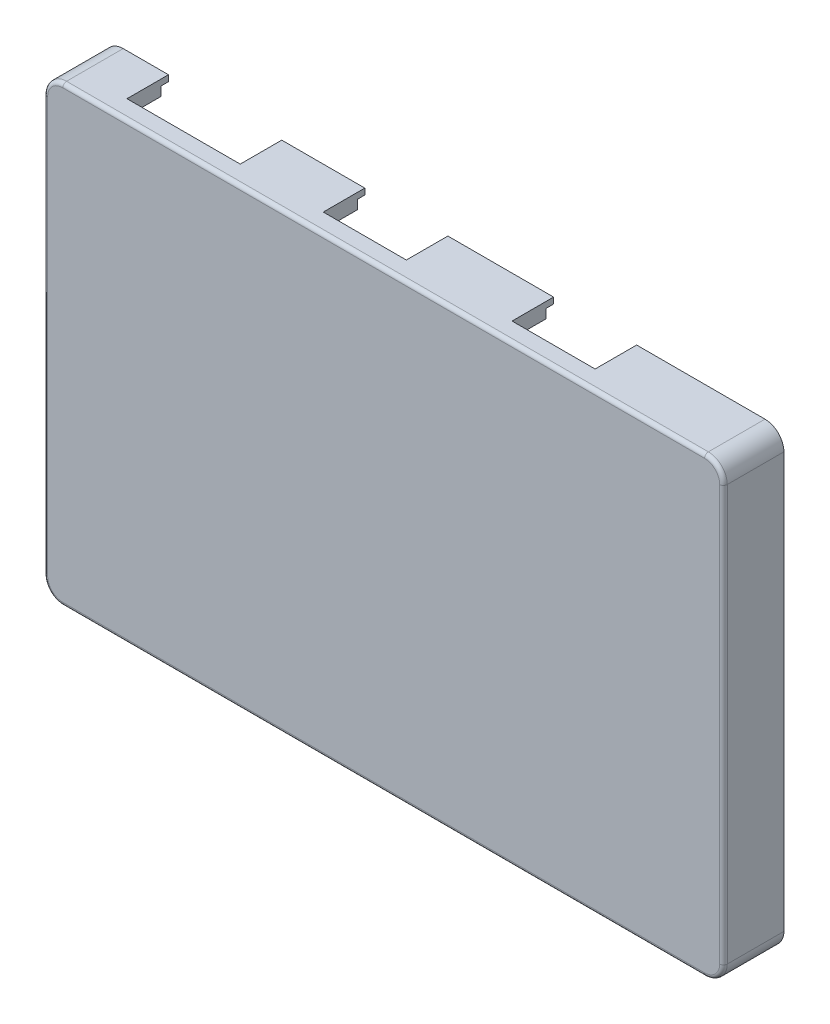
SolidWorks part; units mm, degrees
ref_plane "Спереди" through (0, 0, 0) normal (0, 0, 1) x (1, 0, 0)
ref_plane "Сверху" through (0, 0, 0) normal (0, 1, 0) x (1, 0, 0)
ref_plane "Справа" through (0, 0, 0) normal (1, 0, 0) x (0, 0, -1)
sketch "Эскиз1" plane through (0, 0, 0) normal (0, 0, 1) x (1, 0, 0)
  line L1 (-33.6522, 21.2609) -> (56.3478, 21.2609)
  line L2 (-33.6522, 21.2609) -> (-33.6522, -38.7391)
  line L3 (-33.6522, -38.7391) -> (56.3478, -38.7391)
  line L4 (56.3478, 21.2609) -> (56.3478, -38.7391)
  dimension "D1" = 90
  dimension "D2" = 60
extrude "Бобышка-Вытянуть1" add sketch "Эскиз1" along normal blind 2
sketch "Эскиз2" plane through (0, 0, 0) normal (0, 0, -1) x (-1, 0, 0)
  line L0 (-56.3478, 21.2609) -> (33.6522, 21.2609) construction
  line L1 (28.6522, -16.7391) -> (-21.3478, -16.7391)
  line L2 (28.6522, -16.7391) -> (28.6522, 18.2609)
  line L3 (28.6522, 18.2609) -> (-21.3478, 18.2609)
  line L4 (-21.3478, -16.7391) -> (-21.3478, 18.2609)
  line L5 (33.6522, 21.2609) -> (33.6522, -38.7391) construction
  dimension "D1" = 35
  dimension "D2" = 50
  dimension "D3" = 3
  dimension "D4" = 5
extrude "Бобышка-Вытянуть2" add sketch "Эскиз2" along normal blind 1
sketch "Эскиз3" plane through (0, 0, -1) normal (0, 0, -1) x (-1, 0, 0)
  line L0 (28.6522, -16.7391) -> (28.6522, 18.2609) construction
  line L1 (24.6522, -0.7391) -> (10.6522, -0.7391)
  line L2 (24.6522, -0.7391) -> (24.6522, 12.2609)
  line L3 (24.6522, 12.2609) -> (10.6522, 12.2609)
  line L4 (10.6522, -0.7391) -> (10.6522, 12.2609)
  line L5 (28.6522, 18.2609) -> (-21.3478, 18.2609) construction
  dimension "D1" = 14
  dimension "D2" = 13
  dimension "D3" = 4
  dimension "D4" = 6
extrude "Бобышка-Вытянуть3" add sketch "Эскиз3" along normal blind 10
sketch "Эскиз4" plane through (0, 0, -1) normal (0, 0, -1) x (-1, 0, 0)
  line L0 (28.6522, 18.2609) -> (-21.3478, 18.2609) construction
  line L1 (-1.3478, 9.2609) -> (-11.3478, 9.2609)
  line L2 (-1.3478, 9.2609) -> (-1.3478, 21.2609)
  line L3 (-1.3478, 21.2609) -> (-11.3478, 21.2609)
  line L4 (-11.3478, 9.2609) -> (-11.3478, 21.2609)
  line L5 (28.6522, -16.7391) -> (28.6522, 18.2609) construction
  dimension "D1" = 10
  dimension "D2" = 12
  dimension "D3" = 3
  dimension "D4" = 30
extrude "Бобышка-Вытянуть4" add sketch "Эскиз4" along normal blind 5
sketch "Эскиз5" plane through (0, 0, 0) normal (0, 0, -1) x (-1, 0, 0)
  line L0 (-56.3478, -38.7391) -> (-56.3478, 21.2609) construction
  line L1 (-25.3478, -7.7391) -> (-51.3478, -7.7391)
  line L2 (-25.3478, -7.7391) -> (-25.3478, 18.2609)
  line L3 (-25.3478, 18.2609) -> (-51.3478, 18.2609)
  line L4 (-51.3478, -7.7391) -> (-51.3478, 18.2609)
  line L5 (-56.3478, 21.2609) -> (33.6522, 21.2609) construction
  dimension "D1" = 26
  dimension "D2" = 26
  dimension "D3" = 5
  dimension "D4" = 3
extrude "Бобышка-Вытянуть5" add sketch "Эскиз5" along normal blind 1
sketch "Эскиз6" plane through (0, 0, -1) normal (0, 0, -1) x (-1, 0, 0)
  line L0 (-25.3478, -7.7391) -> (-25.3478, 18.2609) construction
  line L1 (-26.3478, 9.2609) -> (-36.3478, 9.2609)
  line L2 (-26.3478, 9.2609) -> (-26.3478, 19.2609)
  line L3 (-26.3478, 19.2609) -> (-36.3478, 19.2609)
  line L4 (-36.3478, 9.2609) -> (-36.3478, 19.2609)
  line L5 (-25.3478, 18.2609) -> (-51.3478, 18.2609) construction
  dimension "D1" = 10
  dimension "D2" = 10
  dimension "D3" = 1
  dimension "D4" = 1
extrude "Бобышка-Вытянуть6" add sketch "Эскиз6" along normal blind 7
sketch "Эскиз7" plane through (0, 0, 0) normal (0, 0, -1) x (-1, 0, 0)
  line L0 (-21.3478, -16.7391) -> (28.6522, -16.7391) construction
  line L1 (6.8938, -35.7391) -> (-36.1062, -35.7391)
  line L2 (6.8938, -35.7391) -> (6.8938, -17.7391)
  line L3 (6.8938, -17.7391) -> (-36.1062, -17.7391)
  line L4 (-36.1062, -35.7391) -> (-36.1062, -17.7391)
  dimension "D1" = 18
  dimension "D2" = 43
  dimension "D3" = 1
extrude "Бобышка-Вытянуть7" add sketch "Эскиз7" along normal blind 1
sketch "Эскиз8" plane through (0, 0, 0) normal (0, 0, -1) x (-1, 0, 0)
  line L0 (33.6522, -38.7391) -> (-56.3478, -38.7391) construction
  line L1 (-56.3478, -38.7391) -> (-54.3478, -38.7391)
  line L2 (-56.3478, -38.7391) -> (-56.3478, 21.2609)
  line L3 (-56.3478, 21.2609) -> (-54.3478, 21.2609)
  line L4 (-54.3478, -38.7391) -> (-54.3478, 21.2609)
  line L5 (-56.3478, 21.2609) -> (33.6522, 21.2609) construction
  line L6 (-56.3478, -38.7391) -> (-56.3478, 21.2609) construction
  point P10 (0, 0)
  dimension "D1" = 2
  dimension "D2" = 0
  dimension "D3" = 0
  dimension "D4" = 0
extrude "Бобышка-Вытянуть8" add sketch "Эскиз8" along normal blind 5
sketch "Эскиз9" plane through (0, 0, 0) normal (0, 0, -1) x (-1, 0, 0)
  line L0 (-54.3478, -38.7391) -> (-54.3478, 21.2609) construction
  line L1 (-54.3478, -38.7391) -> (33.6522, -38.7391)
  line L2 (-54.3478, -38.7391) -> (-54.3478, -36.7391)
  line L3 (-54.3478, -36.7391) -> (33.6522, -36.7391)
  line L4 (33.6522, -38.7391) -> (33.6522, -36.7391)
  line L5 (33.6522, -38.7391) -> (-54.3478, -38.7391) construction
  line L6 (33.6522, 21.2609) -> (33.6522, -38.7391) construction
  dimension "D1" = 2
  dimension "D2" = 0
  dimension "D3" = 0
  dimension "D4" = 0
extrude "Бобышка-Вытянуть9" add sketch "Эскиз9" along normal blind 5
sketch "Эскиз10" plane through (0, 0, 0) normal (0, 0, -1) x (-1, 0, 0)
  line L0 (33.6522, -36.7391) -> (-54.3478, -36.7391) construction
  line L1 (31.6522, -36.7391) -> (33.6522, -36.7391)
  line L2 (31.6522, -36.7391) -> (31.6522, 21.2609)
  line L3 (31.6522, 21.2609) -> (33.6522, 21.2609)
  line L4 (33.6522, -36.7391) -> (33.6522, 21.2609)
  line L5 (33.6522, 21.2609) -> (33.6522, -36.7391) construction
  line L6 (-54.3478, 21.2609) -> (33.6522, 21.2609) construction
  dimension "D1" = 2
  dimension "D2" = 0
  dimension "D3" = 0
  dimension "D4" = 0
extrude "Бобышка-Вытянуть10" add sketch "Эскиз10" along normal blind 5
sketch "Эскиз11" plane through (0, 0, 0) normal (0, 0, -1) x (-1, 0, 0)
  line L0 (-54.3478, -36.7391) -> (-54.3478, 21.2609) construction
  line L1 (-54.3478, 19.2609) -> (31.6522, 19.2609)
  line L2 (-54.3478, 19.2609) -> (-54.3478, 21.2609)
  line L3 (-54.3478, 21.2609) -> (31.6522, 21.2609)
  line L4 (31.6522, 19.2609) -> (31.6522, 21.2609)
  line L5 (-54.3478, 21.2609) -> (31.6522, 21.2609) construction
  line L6 (31.6522, 21.2609) -> (31.6522, -36.7391) construction
  dimension "D1" = 2
  dimension "D2" = 0
  dimension "D3" = 0
  dimension "D4" = 0
extrude "Бобышка-Вытянуть11" add sketch "Эскиз11" along normal blind 5
sketch "Эскиз12" plane through (0, 0, -5) normal (0, 0, -1) x (-1, 0, 0)
  line L0 (-56.3478, -38.7391) -> (33.6522, -38.7391) construction
  line L1 (-56.3478, -38.7391) -> (-55.5478, -38.7391)
  line L2 (-56.3478, -38.7391) -> (-56.3478, 21.2609)
  line L3 (-56.3478, 21.2609) -> (-55.5478, 21.2609)
  line L4 (-55.5478, -38.7391) -> (-55.5478, 21.2609)
  line L5 (-56.3478, 21.2609) -> (-56.3478, -38.7391) construction
  line L6 (-56.3478, 21.2609) -> (33.6522, 21.2609) construction
  dimension "D1" = 0.8
  dimension "D2" = 0
  dimension "D3" = 0
  dimension "D4" = 0
extrude "Бобышка-Вытянуть12" add sketch "Эскиз12" along normal blind 1
sketch "Эскиз13" plane through (0, 0, -5) normal (0, 0, -1) x (-1, 0, 0)
  line L0 (-55.5478, -38.7391) -> (33.6522, -38.7391) construction
  line L1 (-55.5478, -38.7391) -> (33.6522, -38.7391)
  line L2 (-55.5478, -38.7391) -> (-55.5478, -37.9391)
  line L3 (-55.5478, -37.9391) -> (33.6522, -37.9391)
  line L4 (33.6522, -38.7391) -> (33.6522, -37.9391)
  line L5 (-55.5478, -38.7391) -> (-55.5478, 21.2609) construction
  line L6 (33.6522, -38.7391) -> (33.6522, 21.2609) construction
  dimension "D1" = 0.8
  dimension "D2" = 0
  dimension "D3" = 0
  dimension "D4" = 0
extrude "Бобышка-Вытянуть13" add sketch "Эскиз13" along normal blind 1
sketch "Эскиз14" plane through (0, 0, -5) normal (0, 0, -1) x (-1, 0, 0)
  line L0 (33.6522, -37.9391) -> (-55.5478, -37.9391) construction
  line L1 (32.8522, -37.9391) -> (33.6522, -37.9391)
  line L2 (32.8522, -37.9391) -> (32.8522, 21.2609)
  line L3 (32.8522, 21.2609) -> (33.6522, 21.2609)
  line L4 (33.6522, -37.9391) -> (33.6522, 21.2609)
  line L5 (33.6522, -37.9391) -> (33.6522, 21.2609) construction
  line L6 (33.6522, 21.2609) -> (-1.3478, 21.2609) construction
  dimension "D1" = 0.8
  dimension "D2" = 0
  dimension "D3" = 0
  dimension "D4" = 0
extrude "Бобышка-Вытянуть14" add sketch "Эскиз14" along normal blind 1
sketch "Эскиз15" plane through (0, 0, -5) normal (0, 0, -1) x (-1, 0, 0)
  line L0 (-55.5478, -37.9391) -> (-55.5478, 21.2609) construction
  line L1 (-55.5478, 20.4609) -> (32.8522, 20.4609)
  line L2 (-55.5478, 20.4609) -> (-55.5478, 21.2609)
  line L3 (-55.5478, 21.2609) -> (32.8522, 21.2609)
  line L4 (32.8522, 20.4609) -> (32.8522, 21.2609)
  line L5 (-11.3478, 21.2609) -> (-55.5478, 21.2609) construction
  line L6 (32.8522, 21.2609) -> (32.8522, -37.9391) construction
  dimension "D1" = 0.8
  dimension "D2" = 0
  dimension "D3" = 0
  dimension "D4" = 0
extrude "Бобышка-Вытянуть15" add sketch "Эскиз15" along normal blind 1
sketch "Эскиз16" plane through (0, 9.2609, 0) normal (0, -1, 0) x (1, 0, 0)
  line L0 (36.3478, -8) -> (36.3478, -1) construction
  line L1 (36.8478, -0.5) -> (25.8478, -0.5)
  line L2 (36.8478, -0.5) -> (36.8478, -8.5)
  line L3 (36.8478, -8.5) -> (25.8478, -8.5)
  line L4 (25.8478, -0.5) -> (25.8478, -8.5)
  line L5 (36.3478, -1) -> (26.3478, -1) construction
  line L6 (36.3478, -8) -> (26.3478, -8) construction
  line L7 (26.3478, -8) -> (26.3478, -1) construction
  dimension "D1" = 0.5
  dimension "D2" = 0.5
  dimension "D3" = 0.5
  dimension "D4" = 0.5
extrude "Вырез-Вытянуть2" cut sketch "Эскиз16" against normal blind 34 contours L2 L3 L4 L1
sketch "Эскиз17" plane through (0, 9.2609, 0) normal (0, -1, 0) x (1, 0, 0)
  line L0 (11.3478, -1) -> (1.3478, -1) construction
  line L1 (11.8478, -0.5) -> (0.8478, -0.5)
  line L2 (11.8478, -0.5) -> (11.8478, -6.5)
  line L3 (11.8478, -6.5) -> (0.8478, -6.5)
  line L4 (0.8478, -0.5) -> (0.8478, -6.5)
  line L5 (11.3478, -6) -> (11.3478, -1) construction
  line L6 (11.3478, -6) -> (1.3478, -6) construction
  line L7 (1.3478, -6) -> (1.3478, -1) construction
  dimension "D1" = 0.5
  dimension "D2" = 0.5
  dimension "D3" = 0.5
  dimension "D4" = 0.5
extrude "Вырез-Вытянуть3" cut sketch "Эскиз17" against normal blind 34
sketch "Эскиз18" plane through (0, -0.7391, 0) normal (0, -1, 0) x (1, 0, 0)
  line L0 (-10.6522, -11) -> (-10.6522, -1) construction
  line L1 (-10.1522, -0.5) -> (-25.1522, -0.5)
  line L2 (-10.1522, -0.5) -> (-10.1522, -11.5)
  line L3 (-10.1522, -11.5) -> (-25.1522, -11.5)
  line L4 (-25.1522, -0.5) -> (-25.1522, -11.5)
  line L5 (-10.6522, -1) -> (-24.6522, -1) construction
  line L6 (-10.6522, -11) -> (-24.6522, -11) construction
  line L7 (-24.6522, -11) -> (-24.6522, -1) construction
  dimension "D1" = 0.5
  dimension "D2" = 0.5
  dimension "D3" = 0.5
  dimension "D4" = 0.5
extrude "Вырез-Вытянуть4" cut sketch "Эскиз18" against normal blind 34
sketch "Эскиз19" plane through (0, 0, 0) normal (0, 0, -1) x (-1, 0, 0)
  line L0 (-54.3478, -36.7391) -> (-54.3478, 19.2609) construction
  line L1 (-54.3478, -10.2391) -> (-24.3478, -10.2391)
  line L2 (-54.3478, -10.2391) -> (-54.3478, -8.2391)
  line L3 (-54.3478, -8.2391) -> (-24.3478, -8.2391)
  line L4 (-24.3478, -10.2391) -> (-24.3478, -8.2391)
  line L5 (-51.3478, -7.7391) -> (-25.3478, -7.7391) construction
  line L6 (-25.3478, -7.7391) -> (-25.3478, 18.2609) construction
  dimension "D1" = 2
  dimension "D2" = 0
  dimension "D3" = 0.5
  dimension "D4" = 1
extrude "Бобышка-Вытянуть16" add sketch "Эскиз19" along normal blind 2
sketch "Эскиз20" plane through (0, 0, -1) normal (0, 0, -1) x (-1, 0, 0)
  line L1 (-36.1062, -35.7391) -> (6.8938, -35.7391)
  line L2 (-36.1062, -35.7391) -> (-36.1062, -17.7391)
  line L3 (-36.1062, -17.7391) -> (6.8938, -17.7391)
  line L4 (6.8938, -35.7391) -> (6.8938, -17.7391)
extrude "Вырез-Вытянуть5" cut sketch "Эскиз20" against normal blind 1.5
sketch "Эскиз21" plane through (0, 0, -1) normal (0, 0, -1) x (-1, 0, 0)
  line L1 (-51.3478, -7.7391) -> (-25.3478, -7.7391)
  line L2 (-51.3478, -7.7391) -> (-51.3478, 18.2609)
  line L3 (-51.3478, 18.2609) -> (-25.3478, 18.2609)
  line L4 (-25.3478, -7.7391) -> (-25.3478, 18.2609)
extrude "Вырез-Вытянуть6" cut sketch "Эскиз21" against normal blind 1.5
sketch "Эскиз22" plane through (0, 0, -1) normal (0, 0, -1) x (-1, 0, 0)
  line L1 (-21.3478, -16.7391) -> (28.6522, -16.7391)
  line L2 (-21.3478, -16.7391) -> (-21.3478, 18.2609)
  line L3 (-21.3478, 18.2609) -> (28.6522, 18.2609)
  line L4 (28.6522, -16.7391) -> (28.6522, 18.2609)
extrude "Вырез-Вытянуть7" cut sketch "Эскиз22" against normal blind 1.5
fillet "Скругление1" radius 2.5 8 edges at (54.3478, -36.7391, -2.5) (54.3478, 19.2609, -2.5) (-31.6522, -36.7391, -2.5) (-31.6522, 19.2609, -2.5) (56.3478, 21.2609, -2) (56.3478, -38.7391, -2) (-33.6522, -38.7391, -2) (-33.6522, 21.2609, -2)
fillet "Скругление2" radius 2.5 4 edges at (55.5478, -37.9391, -5.5) (55.5478, 20.4609, -5.5) (-32.8522, -37.9391, -5.5) (-32.8522, 20.4609, -5.5)
fillet "Скругление3" radius 0.5 8 edges at (55.6156, -38.0069, 2) (11.3478, -38.7391, 2) (-32.9199, -38.0069, 2) (-33.6522, -8.7391, 2) (-32.9199, 20.5286, 2) (11.3478, 21.2609, 2) (55.6156, 20.5286, 2) (56.3478, -8.7391, 2)
